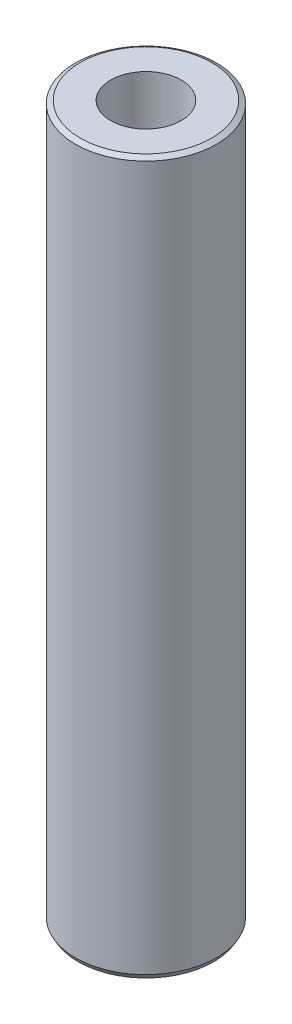
SolidWorks part; units mm, degrees
ref_plane "Front Plane" through (0, 0, 0) normal (0, 0, 1) x (1, 0, 0)
ref_plane "Top Plane" through (0, 0, 0) normal (0, 1, 0) x (1, 0, 0)
ref_plane "Right Plane" through (0, 0, 0) normal (1, 0, 0) x (0, 0, -1)
sketch "Sketch2" plane through (0, 0, 0) normal (0, 1, 0) x (1, 0, 0)
  circle A0 centre (0, 0) radius 2.5
  dimension "D1" = 5
extrude "Boss-Extrude1" add sketch "Sketch2" along normal blind 25.25
chamfer "Chamfer1" distance 0.1 angle 60 2 edges at (0, 0, 2.5) (0, 25.25, 2.5)
hole_wizard "M3x0.5 Tapped Hole1" positions "Sketch3" profile "Sketch4" tap size "M3x0.5" standard "ANSI Metric" end condition through all
sketch "Sketch3" plane through (0, 25.25, 0) normal (0, 1, 0) x (1, 0, 0)
  point P0 (0, 0)
sketch "Sketch4" plane through (0, 25.25, 0) normal (1, 0, 0) x (0, 0, 1)
  line L0 (0, 0) -> (0, 25.25)
  line L1 (0, 25.25) -> (1.25, 25.25)
  line L2 (1.25, 25.25) -> (1.25, 0)
  line L5 (1.25, 0) -> (0, 0)
  line L11 (0, -6.35) -> (0, 107.95) construction
  dimension "Thru Tap Drill Dia." = 2.5
  dimension "Thru Tap Drill Depth" = 25.25
cosmetic thread "Hole Thread1" parameters "D2"=3
